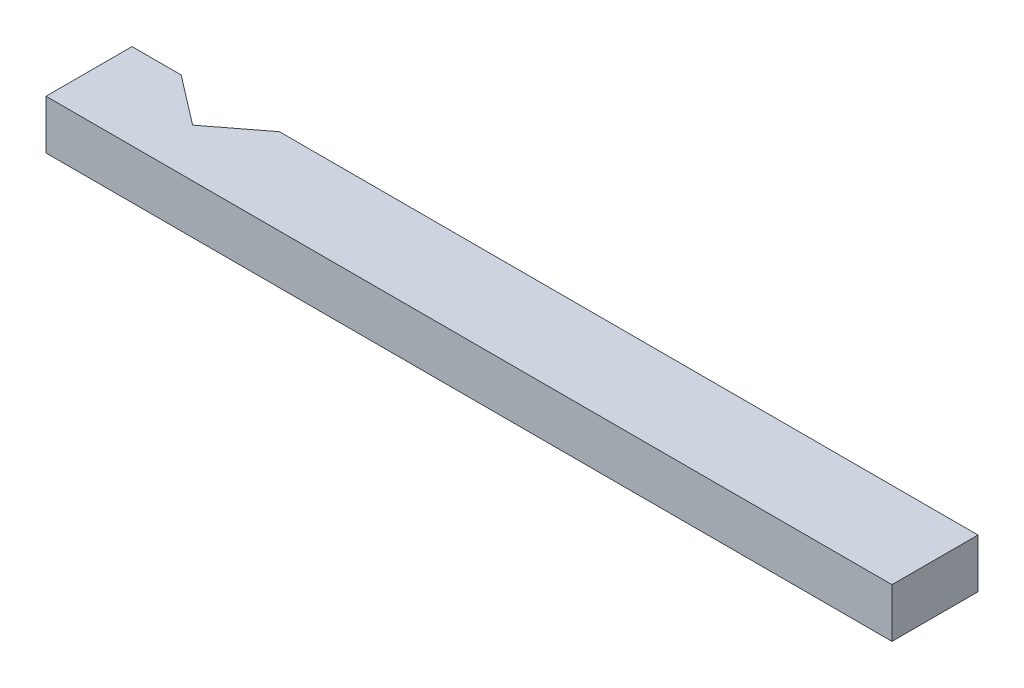
SolidWorks part; units mm, degrees
ref_plane "Front Plane" through (0, 0, 0) normal (0, 0, 1) x (1, 0, 0)
ref_plane "Top Plane" through (0, 0, 0) normal (0, 1, 0) x (1, 0, 0)
ref_plane "Right Plane" through (0, 0, 0) normal (1, 0, 0) x (0, 0, -1)
sketch "Sketch1" plane through (0, 0, 0) normal (0, 1, 0) x (1, 0, 0)
  line L1 (-437.1975, -44.45) -> (437.1975, -44.45)
  line L2 (-437.1975, -44.45) -> (-437.1975, 44.45)
  line L3 (-437.1975, 44.45) -> (437.1975, 44.45)
  line L4 (437.1975, -44.45) -> (437.1975, 44.45)
  line L5 (-437.1975, -44.45) -> (437.1975, 44.45) construction
  line L6 (-437.1975, 44.45) -> (437.1975, -44.45) construction
  point P0 (0, 0)
  dimension "D1" = 88.9
  dimension "D2" = 874.395
extrude "Boss-Extrude1" add sketch "Sketch1" along normal mid plane 50.8
sketch "Sketch2" plane through (0, 25.4, 0) normal (0, 1, 0) x (1, 0, 0)
  line L0 (-386.3975, 44.45) -> (-335.5975, 5.4698)
  line L1 (437.1975, 44.45) -> (-437.1975, 44.45) construction
  line L2 (-335.5975, 5.4698) -> (-284.7975, 44.45)
  line L3 (-386.3975, 44.45) -> (-284.7975, 44.45)
  line L4 (-335.5975, 5.4698) -> (-335.5975, 44.45) construction
  line L5 (-437.1975, 44.45) -> (-437.1975, -44.45) construction
  dimension "D1" = 105
  dimension "D2" = 101.6
  dimension "D3" = 101.6
extrude "Cut-Extrude1" cut sketch "Sketch2" against normal through all
